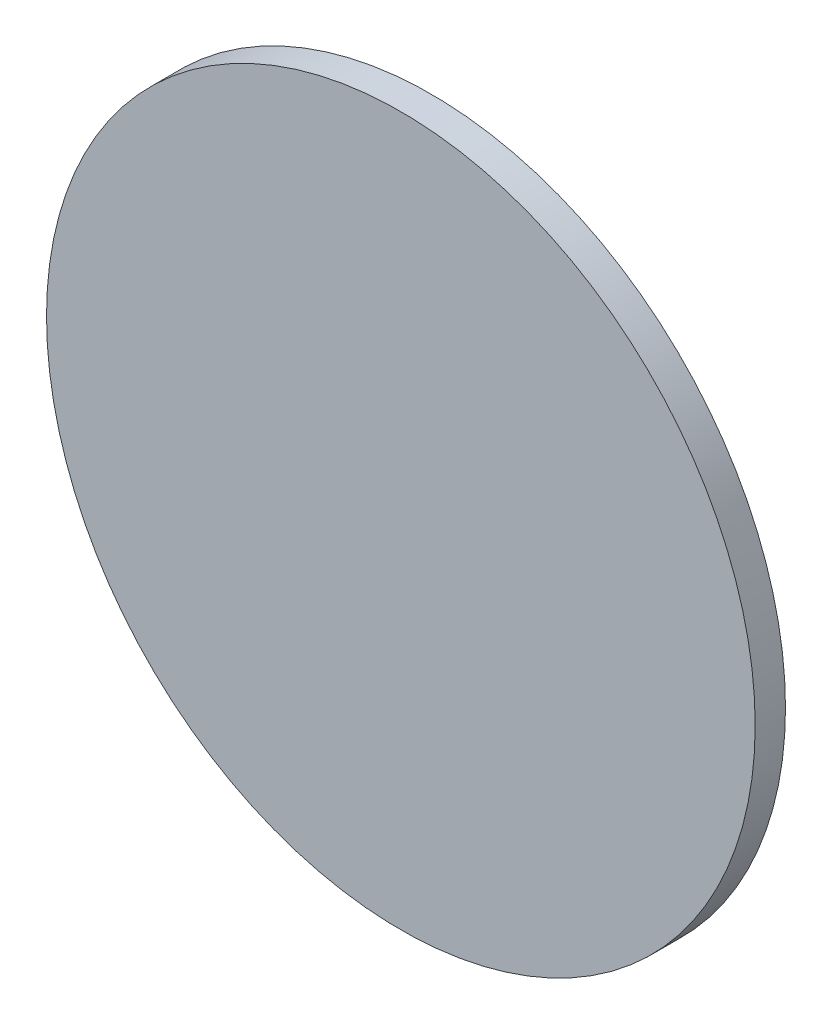
SolidWorks part; units mm, degrees
ref_plane "Front Plane" through (0, 0, 0) normal (0, 0, 1) x (1, 0, 0)
ref_plane "Top Plane" through (0, 0, 0) normal (0, 1, 0) x (1, 0, 0)
ref_plane "Right Plane" through (0, 0, 0) normal (1, 0, 0) x (0, 0, -1)
sketch "Sketch1" plane through (0, 0, 0) normal (0, 0, 1) x (1, 0, 0)
  circle A0 centre (0, 0) radius 74.295
  dimension "D1" = 148.59
extrude "Boss-Extrude1" add sketch "Sketch1" along normal blind 6.35
